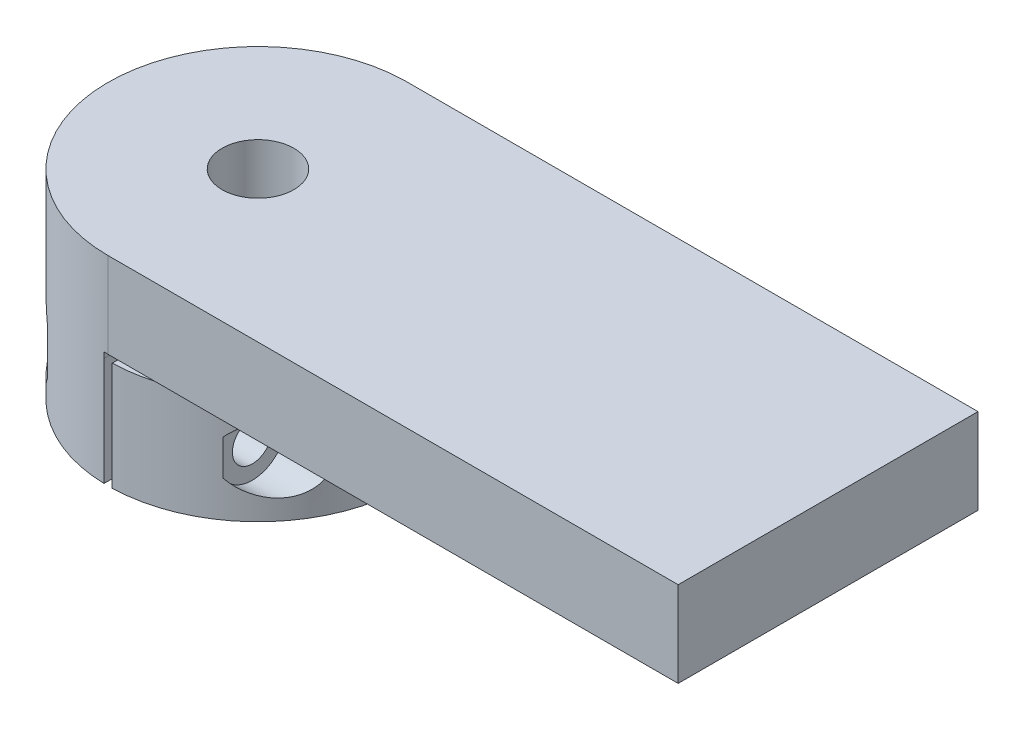
SolidWorks part; units mm, degrees
ref_plane "Front Plane" through (0, 0, 0) normal (0, 0, 1) x (1, 0, 0)
ref_plane "Top Plane" through (0, 0, 0) normal (0, 1, 0) x (1, 0, 0)
ref_plane "Right Plane" through (0, 0, 0) normal (1, 0, 0) x (0, 0, -1)
sketch "Sketch1" plane through (0, 0, 0) normal (0, 1, 0) x (1, 0, 0)
  line L0 (0, 0) -> (0, 11.5924) construction
  line L1 (0, 0) -> (0, -12.2017) construction
  line L2 (19.5999, 0) -> (-19.5999, 0) construction
  line L5 (-0.2625, 3.139) -> (-0.3653, 13.1449)
  line L6 (0.2625, 3.139) -> (0.3653, 13.1449)
  line L7 (-0.2625, -3.139) -> (-0.3653, -13.1449)
  line L8 (0.2625, -3.139) -> (0.3653, -13.1449)
  arc A0 (-0.2625, 3.139) -> (-0.2625, -3.139) centre (0, 0) ccw
  arc A1 (-0.3653, 13.1449) -> (-0.3653, -13.1449) centre (0, 0) ccw
  circle A2 centre (0, 0) radius 13.15 construction
  circle A3 centre (0, 0) radius 3.15 construction
  arc A6 (0.2625, -3.139) -> (0.2625, 3.139) centre (0, 0) ccw
  arc A7 (0.3653, -13.1449) -> (0.3653, 13.1449) centre (0, 0) ccw
  point P9 (0, 0)
  point P13 (0.25, 0)
  point P17 (-0.25, 0)
  dimension "D1" = 6.3
  dimension "D2" = 10
extrude "Boss-Extrude1" add sketch "Sketch1" along normal blind 9.5
ref_plane "Plane1" through (13.15, 0, 0) normal (1, 0, 0) x (0, 0, -1)
sketch "Sketch2" plane through (13.15, 0, 0) normal (1, 0, 0) x (0, 0, -1)
  line L4 (3.139, 0) -> (13.1449, 0)
  line L5 (13.1449, 0) -> (13.1449, 9.5)
  line L6 (13.1449, 9.5) -> (3.139, 9.5)
  line L7 (3.139, 9.5) -> (3.139, 0)
  line L8 (3.139, 0) -> (13.1449, 0) construction
  line L9 (13.1449, 0) -> (13.1449, 9.5) construction
  line L10 (13.1449, 9.5) -> (3.139, 9.5) construction
  line L11 (3.139, 9.5) -> (3.139, 0) construction
  circle A0 centre (8.142, 4.75) radius 3
  point P9 (8.142, 0)
  point P11 (13.1449, 4.75)
  dimension "D2" = 6
  dimension "D1" = 0
extrude "Cut-Extrude1" cut sketch "Sketch2" against normal blind 5.5
sketch "Sketch3" plane through (7.65, 0, 0) normal (1, 0, 0) x (0, 0, -1)
  circle A0 centre (8.142, 4.75) radius 1.75
  circle A1 centre (8.142, 4.75) radius 3 construction
  dimension "D1" = 3.5
extrude "Cut-Extrude2" cut sketch "Sketch3" against normal through all and the other way through all
ref_plane "Plane2" through (0, 9.5, 0) normal (0, 1, 0) x (1, 0, 0)
sketch "Sketch5" plane through (0, 9.5, 0) normal (0, 1, 0) x (1, 0, 0)
  line L0 (0, -13.15) -> (50, -13.15)
  line L1 (50, -13.15) -> (50, 13.1449)
  line L2 (50, 13.1449) -> (-0.3653, 13.1449)
  circle A0 centre (0, 0) radius 3.15
  arc A1 (-0.2625, 3.139) -> (-0.2625, -3.139) centre (0, 0) ccw construction
  arc A2 (0.3653, 13.1449) -> (0, -13.15) centre (0, 0) ccw
  arc A3 (-0.3653, 13.1449) -> (-0.3653, -13.1449) centre (0, 0) ccw construction
  dimension "D1" = 50
extrude "Boss-Extrude2" add sketch "Sketch5" along normal blind 8 contours L2 A2 L0 L1 A0
sketch "Sketch6" plane through (0, 0, -13.1449) normal (0, 0, -1) x (-1, 0, 0)
  line L0 (55, 9.5) -> (-55, 9.5) construction
  line L1 (-50, 9.5) -> (0.3653, 9.5)
  line L2 (-50, 9.5) -> (-50, 10)
  line L3 (-50, 10) -> (0.3653, 10)
  line L4 (0.3653, 9.5) -> (0.3653, 10)
  line L5 (-50, 17.5) -> (-50, 9.5) construction
  line L6 (0.3653, 17.5) -> (0.3653, 9.5) construction
  dimension "D1" = 0.5
extrude "Cut-Extrude3" cut sketch "Sketch6" against normal through all
sketch "Sketch15" plane through (-0.2302, 0, 0.0024) normal (0.9999, 0, -0.0103) x (-0.0103, 0, -0.9999)
  circle A0 centre (8.063, 4.75) radius 1.93
  ellipse E0 centre (8.063, 4.75) end of major axis (8.063, 6.5) minor radius 1.7499 construction
  dimension "D1" = 3.86
extrude "Cut-Extrude12" cut sketch "Sketch15" against normal through all
mirror "Mirror11" about plane through (0, 0, 0) normal (0, 0, 1) of "Cut-Extrude12", "Cut-Extrude2", "Cut-Extrude1"
ref_plane "Plane3" through (-13.15, 0, 0) normal (-1, 0, 0) x (0, 0, 1)
sketch "Sketch16" plane through (-13.15, 0, 0) normal (-1, 0, 0) x (0, 0, 1)
  line L1 (9.7922, 7.75) -> (6.3281, 7.75)
  line L2 (6.3281, 7.75) -> (4.5961, 4.75)
  line L3 (4.5961, 4.75) -> (6.3281, 1.75)
  line L4 (6.3281, 1.75) -> (9.7922, 1.75)
  line L5 (9.7922, 1.75) -> (11.5243, 4.75)
  line L6 (11.5243, 4.75) -> (9.7922, 7.75)
  line L7 (-4.5961, 4.75) -> (-6.3281, 7.75)
  line L8 (-6.3281, 7.75) -> (-9.7922, 7.75)
  line L9 (-9.7922, 7.75) -> (-11.5243, 4.75)
  line L10 (-11.5243, 4.75) -> (-9.7922, 1.75)
  line L11 (-9.7922, 1.75) -> (-6.3281, 1.75)
  line L12 (-6.3281, 1.75) -> (-4.5961, 4.75)
  line L14 (-13.1449, 0) -> (13.1449, 0) construction
  circle A0 centre (8.0602, 4.75) radius 3 construction
  circle A1 centre (-8.0602, 4.75) radius 3 construction
  ellipse E0 centre (8.0602, 4.75) end of major axis (8.0602, 6.68) minor radius 1.9299 construction
  ellipse E1 centre (8.0602, 4.75) end of major axis (8.0602, 6.68) minor radius 1.9299 construction
  ellipse E2 centre (-8.0602, 4.75) end of major axis (-8.0602, 6.68) minor radius 1.9299 construction
  ellipse E3 centre (-8.0602, 4.75) end of major axis (-8.0602, 6.68) minor radius 1.9299 construction
  point P3 (5.4621, 3.25)
  point P32 (0, 0)
  point P40 (11.5243, 4.75)
  dimension "D1" = 6
extrude "Cut-Extrude14" cut sketch "Sketch16" against normal blind 5
